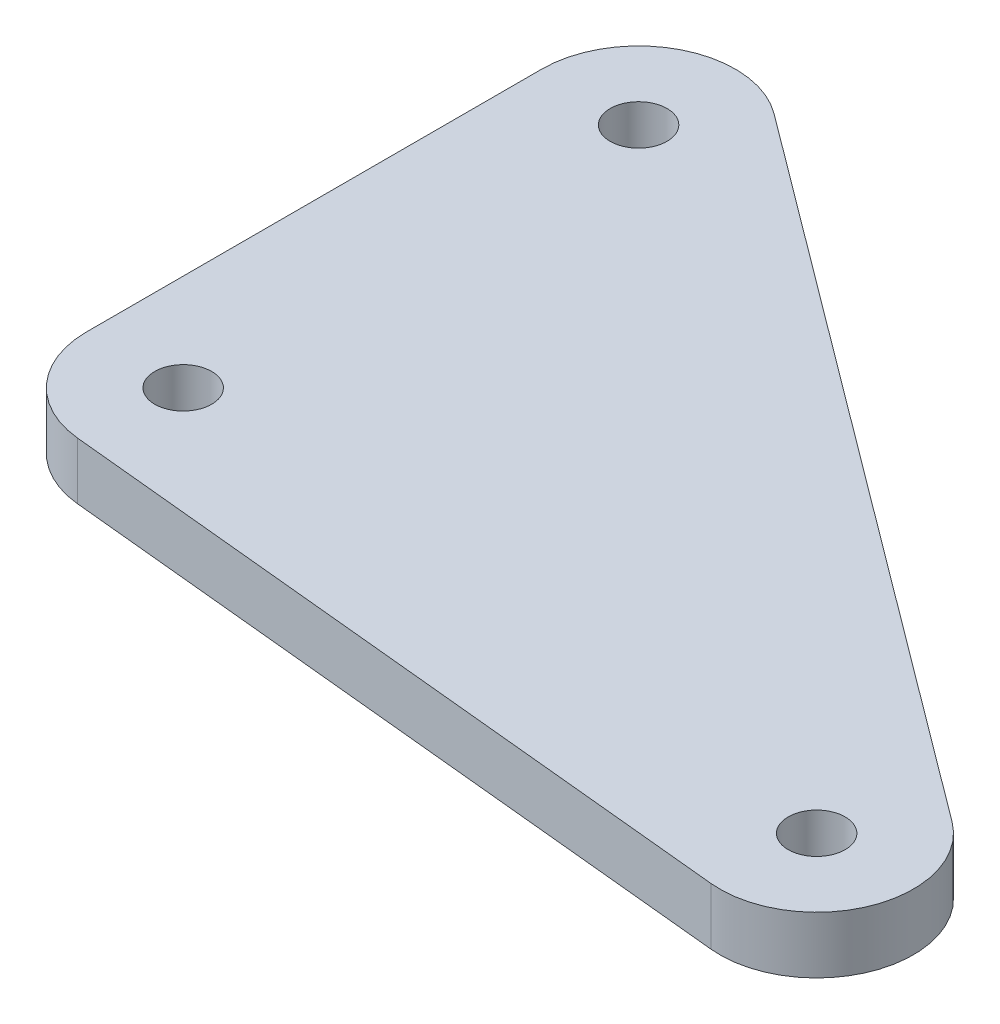
SolidWorks part; units mm, degrees
ref_plane "Front Plane" through (0, 0, 0) normal (0, 0, 1) x (1, 0, 0)
ref_plane "Top Plane" through (0, 0, 0) normal (0, 1, 0) x (1, 0, 0)
ref_plane "Right Plane" through (0, 0, 0) normal (1, 0, 0) x (0, 0, -1)
sketch "Sketch1" plane through (0, 0, 0) normal (0, 1, 0) x (1, 0, 0)
  line L0 (2.5424, 3.4057) -> (33.3939, -19.6256)
  line L1 (30.4359, -27.2609) -> (-0.4156, -24.2296)
  line L3 (-4.25, -20) -> (-4.25, 0)
  circle A0 centre (0, 0) radius 1.25
  circle A1 centre (0, -20) radius 1.25
  circle A2 centre (30.8514, -23.0313) radius 1.25
  arc A3 (2.5424, 3.4057) -> (-4.25, 0) centre (0, 0) ccw
  arc A4 (-4.25, -20) -> (-0.4156, -24.2296) centre (0, -20) ccw
  arc A5 (30.4359, -27.2609) -> (33.3939, -19.6256) centre (30.8514, -23.0313) ccw
  point P7 (0, 0)
  dimension "D1" = 2.5
  dimension "D5" = 3
  dimension "D2" = 20
  dimension "D3" = 38.5
  dimension "D4" = 31
extrude "Boss-Extrude1" add sketch "Sketch1" along normal blind 2.5
